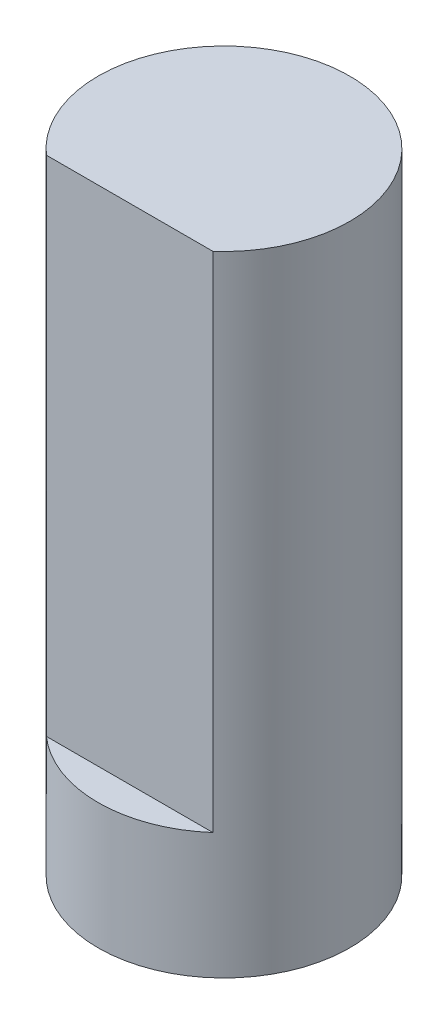
SolidWorks part; units mm, degrees
ref_plane "Front Plane" through (0, 0, 0) normal (0, 0, 1) x (1, 0, 0)
ref_plane "Top Plane" through (0, 0, 0) normal (0, 1, 0) x (1, 0, 0)
ref_plane "Right Plane" through (0, 0, 0) normal (1, 0, 0) x (0, 0, -1)
sketch "Sketch2" plane through (0, 0, 0) normal (0, 1, 0) x (1, 0, 0)
  circle A0 centre (0, 0) radius 2
  dimension "D1" = 4
extrude "Boss-Extrude1" add sketch "Sketch2" along normal blind 10
sketch "Sketch3" plane through (0, 10, 0) normal (0, 1, 0) x (1, 0, 0)
  line L0 (-1.3229, -1.5) -> (1.3229, -1.5)
  line L1 (0, 0) -> (0.9149, 0) construction
  circle A0 centre (0, 0) radius 2 construction
  arc A1 (-1.3229, -1.5) -> (1.3229, -1.5) centre (0, 0) ccw
  dimension "D1" = 1.5
extrude "Cut-Extrude1" cut sketch "Sketch3" against normal blind 8
